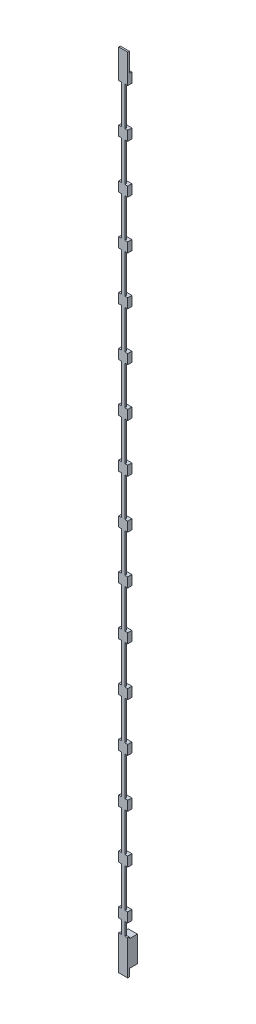
SolidWorks part; units mm, degrees
ref_plane "Front Plane" through (0, 0, 0) normal (0, 0, 1) x (1, 0, 0)
ref_plane "Top Plane" through (0, 0, 0) normal (0, 1, 0) x (1, 0, 0)
ref_plane "Right Plane" through (0, 0, 0) normal (1, 0, 0) x (0, 0, -1)
sketch "Sketch2" plane through (0, 0, 0) normal (0, 0, 1) x (1, 0, 0)
  line L0 (-2.79, 0) -> (2.79, 0)
  line L1 (-2.79, 0) -> (-2.79, 21.51)
  line L2 (2.79, 0) -> (2.79, 21.51)
  line L3 (-2.79, 21.51) -> (2.79, 21.51)
  dimension "D1" = 5.58
  dimension "D2" = 21.51
extrude "Boss-Extrude1" add sketch "Sketch2" along normal mid plane 1
sketch "Sketch3" plane through (0, 0, 0) normal (0, 0, 1) x (1, 0, 0)
  line L0 (-2.79, 35.51) -> (2.79, 35.51)
  line L1 (-2.79, 35.51) -> (-2.79, 29.51)
  line L2 (2.79, 35.51) -> (2.79, 29.51)
  line L3 (-2.79, 29.51) -> (-1, 29.51)
  line L4 (1, 29.51) -> (2.79, 29.51)
  line L5 (-1, 29.51) -> (-1, 4.51)
  line L6 (1, 29.51) -> (1, 4.51)
  line L7 (-1, 4.51) -> (1, 4.51)
  line L8 (0, 0) -> (0, 32.51) construction
  line L9 (-2.79, 35.51) -> (2.79, 29.51) construction
  line L10 (-2.79, 0) -> (2.79, 0) construction
  dimension "D1" = 5.58
  dimension "D2" = 2
  dimension "D3" = 31
  dimension "D4" = 32.51
  dimension "D5" = 6
extrude "Boss-Extrude2" add sketch "Sketch3" along normal mid plane 1
sketch "Sketch4" plane through (0, 0, 0.5) normal (0, 0, 1) x (1, 0, 0)
  line L0 (-2.79, 35.51) -> (2.79, 35.51)
  line L1 (-2.79, 35.51) -> (-2.79, 29.51)
  line L2 (2.79, 35.51) -> (2.79, 29.51)
  line L3 (-2.79, 29.51) -> (2.79, 29.51)
extrude "Boss-Extrude3" add sketch "Sketch4" against normal blind 2.6
pattern_linear "LPattern1" count 16 spacing 30 along (0, 1, 0) of "Boss-Extrude3", "Boss-Extrude2"
sketch "Sketch5" plane through (0, 485.51, 0) normal (0, 1, 0) x (1, 0, 0)
  line L0 (-2.79, 0.5) -> (2.79, 0.5)
  line L1 (-2.79, 0.5) -> (-2.79, -0.5)
  line L2 (2.79, 0.5) -> (2.79, -0.5)
  line L3 (-2.79, -0.5) -> (2.79, -0.5)
  line L5 (-2.79, -0.5) -> (-2.79, 2.1) construction
  dimension "D1" = 1
extrude "Boss-Extrude4" add sketch "Sketch5" along normal blind 12
sketch "Sketch9" plane through (0, 0, -0.5) normal (0, 0, 1) x (1, 0, 0)
  line L0 (2.79, 0) -> (2.79, 21.51) construction
  line L1 (-2.79, 20.61) -> (2.79, 20.61)
  line L2 (-2.79, 20.61) -> (-2.79, 4.61)
  line L3 (-2.79, 4.61) -> (2.79, 4.61)
  line L4 (2.79, 20.61) -> (2.79, 4.61)
  line L5 (-2.79, 21.51) -> (-2.79, 0) construction
  line L7 (-2.79, 18.11) -> (2.79, 18.11) construction
  line L8 (2.79, 21.51) -> (1, 21.51) construction
  dimension "D1" = 16
  dimension "D2" = 2.5
  dimension "D3" = 3.4
extrude "Boss-Extrude6" add sketch "Sketch9" against normal blind 5
sketch "Sketch10" plane through (0, 0, 0.5) normal (0, 0, 1) x (1, 0, 0)
  line L0 (-2.79, 4.2) -> (-2.79, 0)
  line L2 (-2.79, 21.51) -> (-2.79, 0) construction
  line L3 (-2.79, 0) -> (2.79, 0)
  line L5 (2.79, 0) -> (2.79, 4.2)
  line L6 (2.79, 0) -> (2.79, 21.51) construction
  line L7 (2.79, 4.2) -> (1.79, 1.2)
  line L8 (1.79, 1.2) -> (-1.79, 1.2)
  line L10 (-1.79, 1.2) -> (-2.79, 4.2)
  dimension "D1" = 1.2
  dimension "D2" = 3
  dimension "D3" = 1
extrude "Cut-Extrude1" [suppressed] cut sketch "Sketch10" against normal up to next
